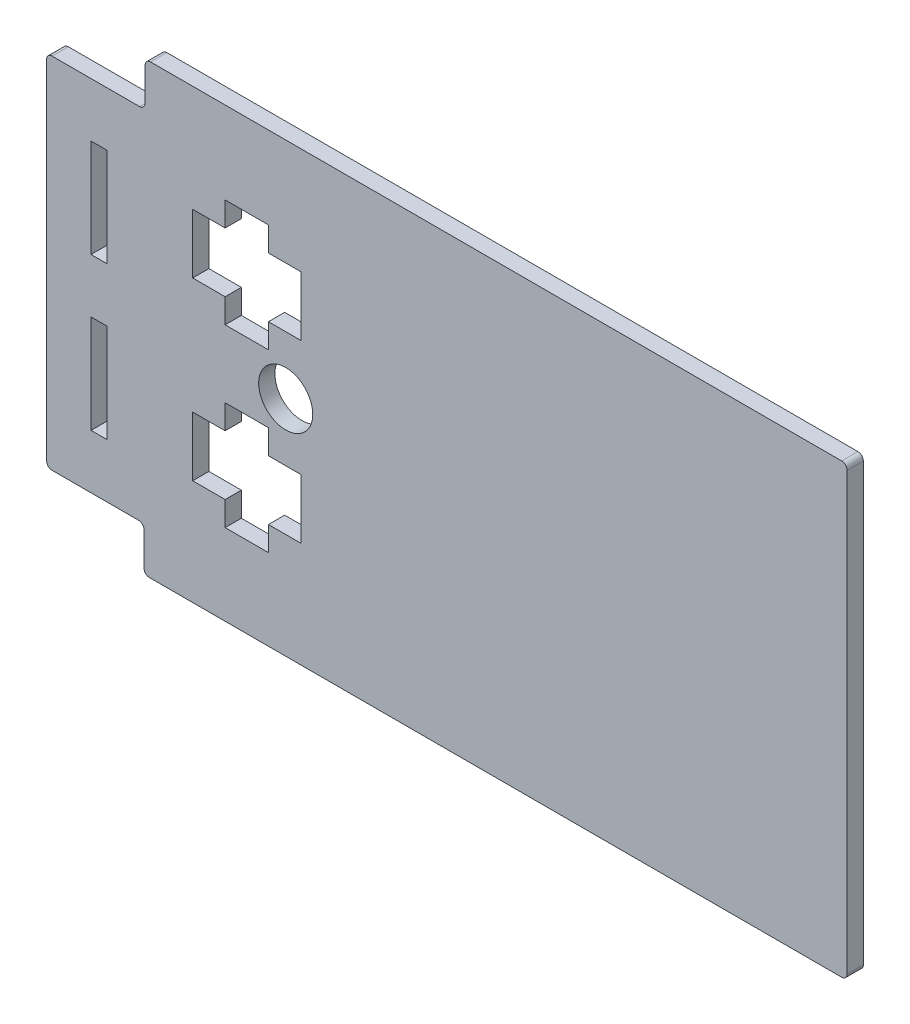
SolidWorks part; units mm, degrees
ref_plane "Alzado" through (0, 0, 0) normal (0, 0, 1) x (1, 0, 0)
ref_plane "Planta" through (0, 0, 0) normal (0, 1, 0) x (1, 0, 0)
ref_plane "Vista lateral" through (0, 0, 0) normal (1, 0, 0) x (0, 0, -1)
sketch "Model" plane through (0, 0, 0) normal (0, 0, 1) x (1, 0, 0)
  line L0 (110.5071, 49.0291) -> (-17.2755, 49.0291)
  line L1 (111.5071, -32.6437) -> (111.5071, 48.0291)
  line L2 (65.1913, -33.6437) -> (110.5071, -33.6437)
  line L3 (32.5071, -33.6437) -> (65.1913, -33.6437)
  line L4 (10.5071, 18.3291) -> (4.5071, 18.3291)
  line L5 (10.5071, -3.1437) -> (4.5071, -3.1437)
  line L6 (10.5071, 29.3291) -> (10.5071, 18.3291)
  line L7 (10.5071, -14.1437) -> (10.5071, -3.1437)
  line L8 (4.5071, 29.3291) -> (10.5071, 29.3291)
  line L9 (32.5071, -33.6437) -> (26.5071, -33.6437)
  line L10 (4.5071, -14.1437) -> (10.5071, -14.1437)
  line L11 (4.5071, 13.8291) -> (4.5071, 18.3291)
  line L12 (4.5071, 1.3563) -> (4.5071, -3.1437)
  line L13 (-3.4929, 13.8291) -> (4.5071, 13.8291)
  line L14 (-3.4929, 1.3563) -> (4.5071, 1.3563)
  line L15 (-3.4929, -3.1437) -> (-3.4929, 1.3563)
  line L16 (-3.4929, 18.3291) -> (-3.4929, 13.8291)
  line L17 (-9.4929, -3.1437) -> (-3.4929, -3.1437)
  line L18 (-9.4929, 18.3291) -> (-3.4929, 18.3291)
  line L19 (-9.4929, -14.1437) -> (-9.4929, -3.1437)
  line L20 (-9.4929, 29.3291) -> (-9.4929, 18.3291)
  line L21 (-3.4929, -14.1437) -> (-9.4929, -14.1437)
  line L22 (-3.4929, 29.3291) -> (-9.4929, 29.3291)
  line L23 (-3.4929, -18.6437) -> (-3.4929, -14.1437)
  line L24 (-3.4929, 33.8291) -> (-3.4929, 29.3291)
  line L25 (4.5071, -18.6437) -> (-3.4929, -18.6437)
  line L26 (4.5071, 33.8291) -> (-3.4929, 33.8291)
  line L27 (4.5071, -14.1437) -> (4.5071, -18.6437)
  line L28 (4.5071, 29.3291) -> (4.5071, 33.8291)
  line L29 (-36.4929, -24.4709) -> (-36.4929, 39.8563)
  line L30 (-28.2929, 12.6927) -> (-25.2929, 12.6927)
  line L31 (-28.2929, 30.8563) -> (-28.2929, 12.6927)
  line L32 (-25.2929, 30.8563) -> (-28.2929, 30.8563)
  line L33 (-25.2929, 12.6927) -> (-25.2929, 30.8563)
  line L34 (-25.2929, 2.6927) -> (-28.2929, 2.6927)
  line L35 (-25.2929, -15.4709) -> (-25.2929, 2.6927)
  line L36 (-28.2929, -15.4709) -> (-25.2929, -15.4709)
  line L37 (-28.2929, 2.6927) -> (-28.2929, -15.4709)
  line L38 (-17.4929, -33.6437) -> (26.5071, -33.6437)
  line L39 (-18.3132, 41.8617) -> (-18.2807, 48.0344)
  line L40 (-18.4929, -26.4709) -> (-18.4929, -32.6437)
  line L41 (-35.4929, 40.8563) -> (-19.3185, 40.867)
  line L42 (-35.4929, -25.4709) -> (-19.4929, -25.4709)
  arc A0 (111.5071, 48.0291) -> (110.5071, 49.0291) centre (110.5071, 48.0291) ccw
  arc A1 (110.5071, -33.6437) -> (111.5071, -32.6437) centre (110.5071, -32.6437) ccw
  arc A2 (-35.4929, 40.8563) -> (-36.4929, 39.8563) centre (-35.4929, 39.8563) ccw
  arc A3 (-36.4929, -24.4709) -> (-35.4929, -25.4709) centre (-35.4929, -24.4709) ccw
  circle A4 centre (7.7071, 7.5927) radius 5
  arc A5 (-17.2755, 49.0291) -> (-18.2807, 48.0344) centre (-17.2808, 48.0291) ccw
  arc A6 (-18.4929, -32.6437) -> (-17.4929, -33.6437) centre (-17.4929, -32.6437) ccw
  arc A7 (-19.3185, 40.867) -> (-18.3132, 41.8617) centre (-19.3132, 41.867) ccw
  arc A8 (-18.4929, -26.4709) -> (-19.4929, -25.4709) centre (-19.4929, -26.4709) ccw
extrude "Saliente-Extruir1" add sketch "Model" along normal blind 3
